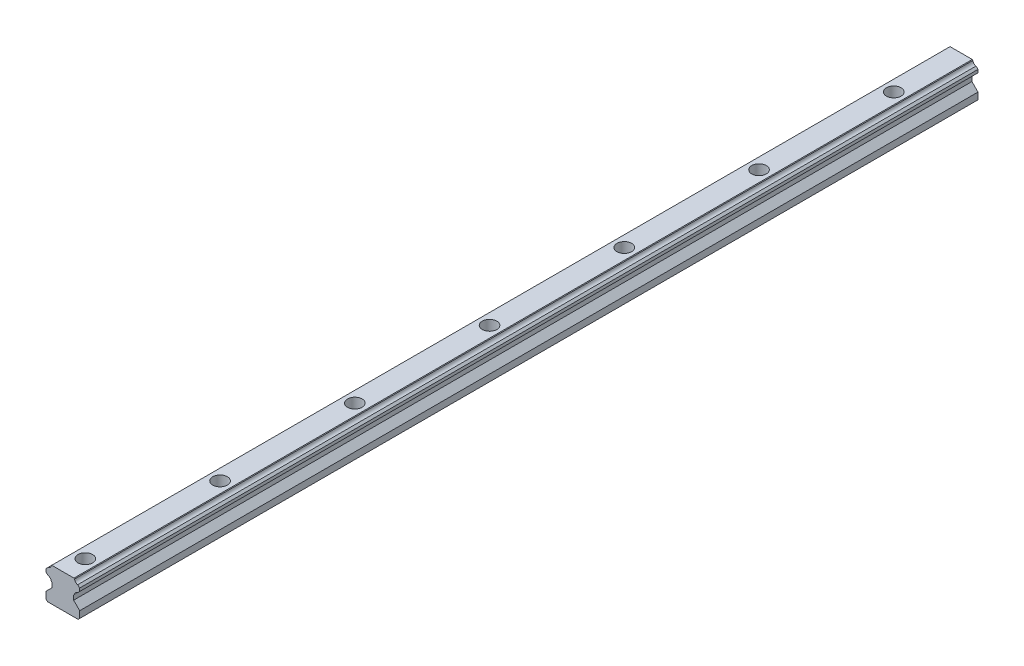
SolidWorks part; units mm, degrees
ref_plane "Спереди" through (0, 0, 0) normal (0, 0, 1) x (1, 0, 0)
ref_plane "Сверху" through (0, 0, 0) normal (0, 1, 0) x (1, 0, 0)
ref_plane "Справа" through (0, 0, 0) normal (1, 0, 0) x (0, 0, -1)
sketch "Model" plane through (0, 0, 0) normal (0, 0, 1) x (1, 0, 0)
  line L7 (6.8, 0) -> (7.5, 0.7)
  line L8 (7.5, 0.7) -> (7.5, 3.6994)
  line L9 (7.5, 3.6994) -> (4.7998, 6.3996)
  line L10 (4.7998, 6.3996) -> (4.7998, 8.4091)
  line L11 (4.7998, 8.4091) -> (5.2008, 8.8101)
  line L12 (6.6481, 10.2574) -> (7.5, 11.1093)
  line L13 (7.5, 11.1093) -> (7.5, 12.4495)
  line L14 (7.5, 12.4495) -> (6.6345, 13.315)
  line L15 (5.2023, 14.7472) -> (4.9495, 15)
  line L16 (4.9495, 15) -> (-4.9495, 15)
  line L17 (-4.9495, 15) -> (-5.2023, 14.7472)
  line L18 (-6.6345, 13.315) -> (-7.5, 12.4495)
  line L19 (-7.5, 12.4495) -> (-7.5, 11.1093)
  line L20 (-7.5, 11.1093) -> (-6.6481, 10.2574)
  line L21 (-5.2008, 8.8101) -> (-4.7998, 8.4091)
  line L22 (-4.7998, 8.4091) -> (-4.7998, 6.3996)
  line L23 (-4.7998, 6.3996) -> (-7.5, 3.6994)
  line L24 (-7.5, 3.6994) -> (-7.5, 0.7)
  line L25 (-7.5, 0.7) -> (-6.8, 0)
  line L26 (-6.8, 0) -> (6.8, 0)
  arc A0 (6.6481, 10.2574) -> (5.2008, 8.8101) centre (6.8215, 8.6367) ccw
  arc A1 (5.2023, 14.7472) -> (6.6345, 13.315) centre (6.8215, 14.9342) ccw
  arc A2 (-6.6345, 13.315) -> (-5.2023, 14.7472) centre (-6.8215, 14.9342) ccw
  arc A3 (-5.2008, 8.8101) -> (-6.6481, 10.2574) centre (-6.8215, 8.6367) ccw
extrude "Бобышка-Вытянуть1" add sketch "Model" along normal blind 400
sketch "Эскиз2" plane through (0, 15, 0) normal (0, 1, 0) x (1, 0, 0)
  line L0 (0, 43.9966) -> (0, -648.9514) construction
  line L1 (4.9495, 0) -> (-4.9495, 0) construction
  circle A0 centre (0, -30) radius 3.25
  circle A1 centre (0, -90) radius 3.25
  circle A2 centre (0, -150) radius 3.25
  circle A3 centre (0, -210) radius 3.25
  circle A4 centre (0, -270) radius 3.25
  circle A5 centre (0, -330) radius 3.25
  circle A6 centre (0, -390) radius 3.25
  circle A7 centre (0, -450) radius 3.25
  circle A8 centre (0, -510) radius 3.25
  circle A9 centre (0, -570) radius 3.25
  dimension "D1" = 10
  dimension "D2" = 30
extrude "Вырез-Вытянуть1" cut sketch "Эскиз2" against normal blind 5.3
sketch "Эскиз3" plane through (0, 9.7, 0) normal (0, 1, 0) x (1, 0, 0)
  circle A0 centre (0, -30) radius 2.25
  circle A1 centre (0, -90) radius 2.25
  circle A2 centre (0, -150) radius 2.25
  circle A3 centre (0, -210) radius 2.25
  circle A4 centre (0, -270) radius 2.25
  circle A5 centre (0, -330) radius 2.25
  circle A6 centre (0, -390) radius 2.25
  circle A7 centre (0, -450) radius 2.25
  circle A8 centre (0, -510) radius 2.25
  circle A9 centre (0, -570) radius 2.25
  dimension "D1" = 10
extrude "Вырез-Вытянуть2" cut sketch "Эскиз3" against normal through all
